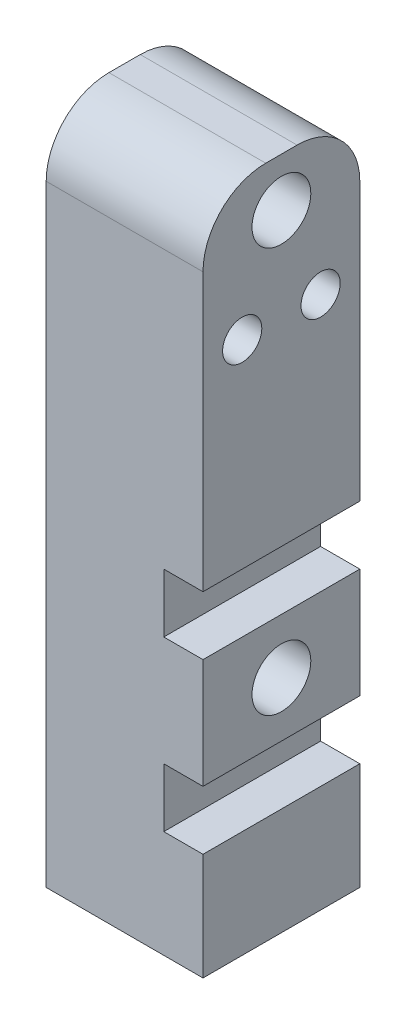
SolidWorks part; units mm, degrees
material "1023 Carbon Steel Sheet (SS)"
ref_plane "Front Plane" through (0, 0, 0) normal (0, 0, 1) x (1, 0, 0)
ref_plane "Top Plane" through (0, 0, 0) normal (0, 1, 0) x (1, 0, 0)
ref_plane "Right Plane" through (0, 0, 0) normal (1, 0, 0) x (0, 0, -1)
sketch "Sketch1" plane through (0, 0, 0) normal (0, 0, 1) x (1, 0, 0)
  line L0 (0, 84.0258) -> (0, -61.0529) construction
  line L1 (0, 0) -> (0, 109.22)
  line L2 (0, 109.22) -> (25.4, 109.22)
  line L3 (25.4, 109.22) -> (25.4, 54.1854)
  line L4 (25.4, 54.1854) -> (19.05, 54.1854)
  line L5 (19.05, 54.1854) -> (19.05, 44.6604)
  line L6 (19.05, 44.6604) -> (25.4, 44.6604)
  line L7 (25.4, 44.6604) -> (25.4, 26.8804)
  line L8 (25.4, 26.8804) -> (19.05, 26.8804)
  line L9 (19.05, 26.8804) -> (19.05, 17.3554)
  line L10 (19.05, 17.3554) -> (25.4, 17.3554)
  line L11 (25.4, 17.3554) -> (25.4, 0)
  line L12 (25.4, 0) -> (0, 0)
  dimension "D1" = 109.22
  dimension "D2" = 9.525
  dimension "D3" = 9.525
  dimension "D4" = 6.35
  dimension "D5" = 6.35
  dimension "D6" = 17.78
  dimension "D7" = 6.35
  dimension "D8" = 25.4
  dimension "D9" = 6.35
  dimension "D10" = 55.0346
extrude "Boss-Extrude1" add sketch "Sketch1" along normal blind 25.4
fillet "Fillet1" radius 10.16 2 edges at (12.7, 109.22, 0) (12.7, 109.22, 25.4)
sketch "Sketch2" plane through (25.4, 0, 0) normal (1, 0, 0) x (0, 0, -1)
  line L2 (-25.4, 35.7704) -> (0, 35.7704) construction
  line L5 (-25.4, 26.8804) -> (-25.4, 44.6604) construction
  line L6 (0, 26.8804) -> (0, 44.6604) construction
  line L7 (-12.7, 44.6604) -> (-12.7, 26.8804) construction
  line L10 (-25.4, 44.6604) -> (0, 44.6604) construction
  line L11 (-25.4, 26.8804) -> (0, 26.8804) construction
  circle A0 centre (-12.7, 35.7704) radius 4.7625
  point P15 (-12.7, 35.7704)
  dimension "D1" = 9.525
  dimension "D2" = 25.4
  dimension "D3" = 17.78
extrude "Cut-Extrude1" cut sketch "Sketch2" against normal blind 25.4
sketch "Sketch4" plane through (25.4, 0, 0) normal (1, 0, 0) x (0, 0, -1)
  line L0 (-12.7, 54.1854) -> (-12.7, 109.22) construction
  line L3 (-25.4, 54.1854) -> (0, 54.1854) construction
  line L4 (-15.24, 109.22) -> (-10.16, 109.22) construction
  line L5 (-25.4, 86.36) -> (0, 86.36) construction
  line L8 (-25.4, 54.1854) -> (-25.4, 99.06) construction
  line L9 (0, 54.1854) -> (0, 99.06) construction
  circle A1 centre (-19.05, 86.36) radius 3.175
  circle A2 centre (-6.35, 86.36) radius 3.175
  dimension "D5" = 6.35
  dimension "D1" = 55.0346
  dimension "D2" = 25.4
  dimension "D3" = 22.86
  dimension "D6" = 12.7
  dimension "D7" = 6.35
extrude "Cut-Extrude3" cut sketch "Sketch4" against normal blind 25.4
sketch "Sketch5" plane through (25.4, 0, 0) normal (1, 0, 0) x (0, 0, -1)
  line L0 (-15.24, 109.22) -> (-10.16, 109.22) construction
  line L1 (-12.7, 109.22) -> (-12.7, 84.9806) construction
  circle A1 centre (-12.7, 101.346) radius 4.7625
  dimension "D1" = 7.874
  dimension "D2" = 9.525
extrude "Cut-Extrude4" cut sketch "Sketch5" against normal blind 16.51
sketch "Sketch6" plane through (0, 0, 0) normal (0, -1, 0) x (1, 0, 0)
  line L0 (25.4, 25.4) -> (25.4, 0) construction
  line L1 (0, 0) -> (25.4, 0) construction
  circle A0 centre (12.7, 12.7) radius 3.175
  point P4 (0, 0)
  point P6 (26.6865, 12.5731)
  dimension "D1" = 6.35
  dimension "D2" = 12.7
  dimension "D3" = 12.7
extrude "Cut-Extrude5" cut sketch "Sketch6" against normal blind 17.78
